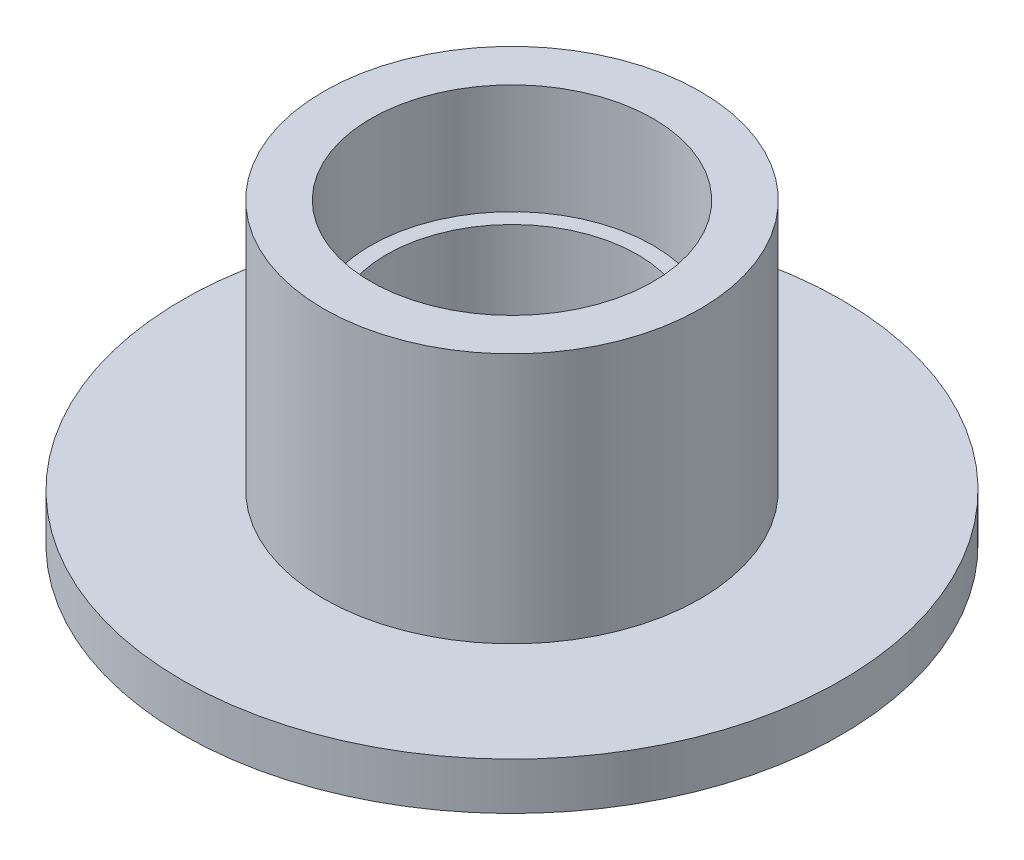
SolidWorks part; units mm, degrees
ref_plane "Plan de face" through (0, 0, 0) normal (0, 0, 1) x (1, 0, 0)
ref_plane "Plan de dessus" through (0, 0, 0) normal (0, 1, 0) x (1, 0, 0)
ref_plane "Plan de droite" through (0, 0, 0) normal (1, 0, 0) x (0, 0, -1)
sketch "Esquisse1" plane through (0, 0, 0) normal (0, 0, 1) x (1, 0, 0)
  line L0 (0, 0) -> (0, 12) construction
  line L1 (-2, 3.8453) -> (-2, 0)
  line L2 (-2, 0) -> (-3, 0)
  line L3 (-3, 0) -> (-3, 3)
  line L4 (-3, 3) -> (-10.5, 3)
  line L5 (-10.5, 3) -> (-10.5, 4.5)
  line L6 (-10.5, 4.5) -> (-6, 4.5)
  line L7 (-6, 4.5) -> (-6, 12.5)
  line L8 (-6, 12.5) -> (-4.5, 12.5)
  line L9 (-4.5, 12.5) -> (-4.5, 9)
  line L10 (-4.5, 9) -> (-4, 9)
  line L11 (-4, 9) -> (-4, 5)
  line L13 (-4, 5) -> (-2, 3.8453)
  dimension "D1" = 4
  dimension "D2" = 6
  dimension "D3" = 21
  dimension "D4" = 12
  dimension "D5" = 9
  dimension "D6" = 8
  dimension "D7" = 3.5
  dimension "D8" = 7.5
  dimension "D9" = 8
  dimension "D10" = 3
  dimension "D11" = 12.5
  dimension "D12" = 120
revolve "Révolution1" add sketch "Esquisse1" angle 360 about L0
